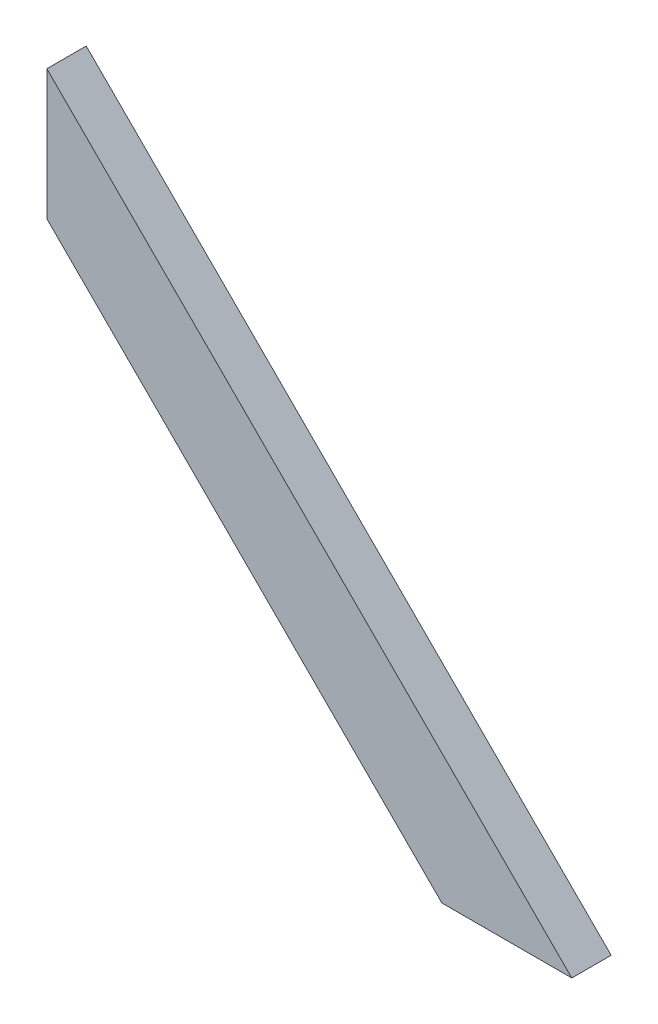
SolidWorks part; units mm, degrees
material "Pine"
ref_plane "Front Plane" through (0, 0, 0) normal (0, 0, 1) x (1, 0, 0)
ref_plane "Top Plane" through (0, 0, 0) normal (0, 1, 0) x (1, 0, 0)
ref_plane "Right Plane" through (0, 0, 0) normal (1, 0, 0) x (0, 0, -1)
sketch "Sketch1" plane through (0, 0, 0) normal (0, 0, 1) x (1, 0, 0)
  line L0 (-140.6266, 473.1159) -> (-140.6266, -34.8841) construction
  line L1 (-140.6266, -34.8841) -> (367.3734, -34.8841) construction
  line L2 (-140.6266, 473.1159) -> (367.3734, -34.8841) construction
  line L3 (-140.6266, 347.3923) -> (241.6498, -34.8841) construction
  line L4 (241.6498, -34.8841) -> (367.3734, -34.8841)
  line L5 (367.3734, -34.8841) -> (-140.6266, 473.1159)
  line L6 (-140.6266, 473.1159) -> (-140.6266, 347.3923)
  line L7 (-140.6266, 347.3923) -> (241.6498, -34.8841)
  dimension "D1" = 508
  dimension "D2" = 508
  dimension "D3" = 88.9
extrude "Boss-Extrude1" add sketch "Sketch1" along normal blind 38.1
